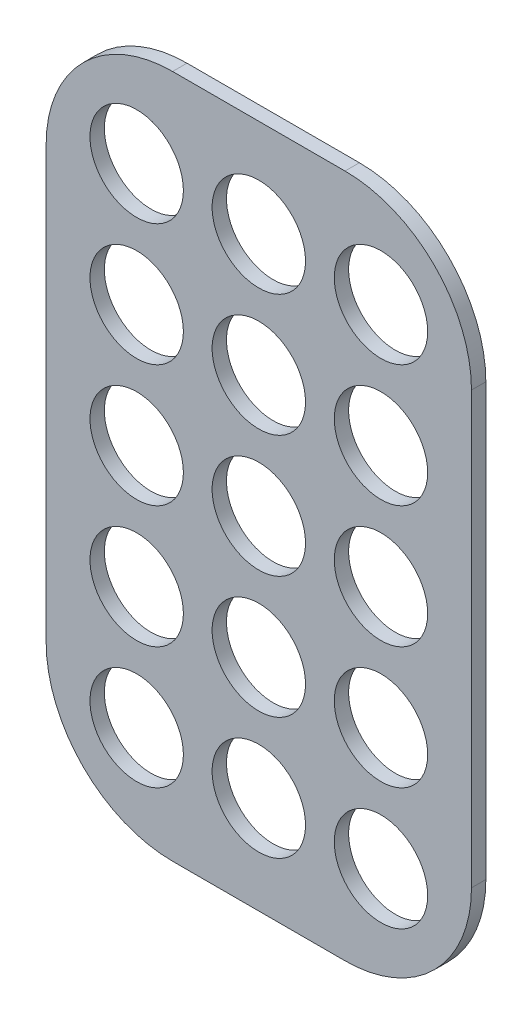
SolidWorks part; units mm, degrees
material "ABS"
ref_plane "Front Plane" through (0, 0, 0) normal (1, 0, 0) x (0, 1, 0)
ref_plane "Top Plane" through (0, 0, 0) normal (0, 0, 1) x (0, 1, 0)
ref_plane "Right Plane" through (0, 0, 0) normal (0, 1, 0) x (-1, 0, 0)
sketch "Sketch1" plane through (0, 0, 0) normal (0, 0, 1) x (0, 1, 0)
  line L1 (-47.6, 59.2) -> (47.6, 59.2)
  line L2 (-47.6, 59.2) -> (-47.6, 0)
  line L3 (-47.6, 0) -> (47.6, 0)
  line L4 (47.6, 59.2) -> (47.6, 0)
  dimension "D1" = 59.2
  dimension "D2" = 95.2
  dimension "D3" = 47.6
extrude "Boss-Extrude1" add sketch "Sketch1" along normal blind 2
sketch "Sketch2" plane through (0, 0, 2) normal (0, 0, 1) x (1, 0, 0)
  line L0 (-59.2, 47.6) -> (-59.2, -47.6) construction
  line L2 (0, 47.6) -> (-59.2, 47.6) construction
  circle A0 centre (-29.6, 0) radius 6.5
  circle A1 centre (-46.6, 0) radius 6.5
  circle A2 centre (-12.6, 0) radius 6.5
  circle A3 centre (-12.6, -17) radius 6.5
  circle A4 centre (-46.6, -17) radius 6.5
  circle A5 centre (-29.6, -17) radius 6.5
  circle A6 centre (-12.6, -34) radius 6.5
  circle A7 centre (-46.6, -34) radius 6.5
  circle A8 centre (-29.6, -34) radius 6.5
  circle A9 centre (-46.6, 17) radius 6.5
  circle A10 centre (-29.6, 17) radius 6.5
  circle A11 centre (-12.6, 17) radius 6.5
  circle A12 centre (-46.6, 34) radius 6.5
  circle A13 centre (-29.6, 34) radius 6.5
  circle A14 centre (-12.6, 34) radius 6.5
  dimension "D1" = 13
  dimension "D2" = 29.6
  dimension "D3" = 47.6
  dimension "D4" = 2
  dimension "D5" = 2
  dimension "D6" = 3
  dimension "D7" = 3
sketch "Sketch3" plane through (0, 0, 2) normal (0, 0, 1) x (1, 0, 0)
extrude "Cut-Extrude2" cut sketch "Sketch2" against normal through all both and the other way through all
fillet "Fillet1" radius 17.6 4 edges at (-59.2, -47.6, 1) (0, -47.6, 1) (-59.2, 47.6, 1) (0, 47.6, 1)
